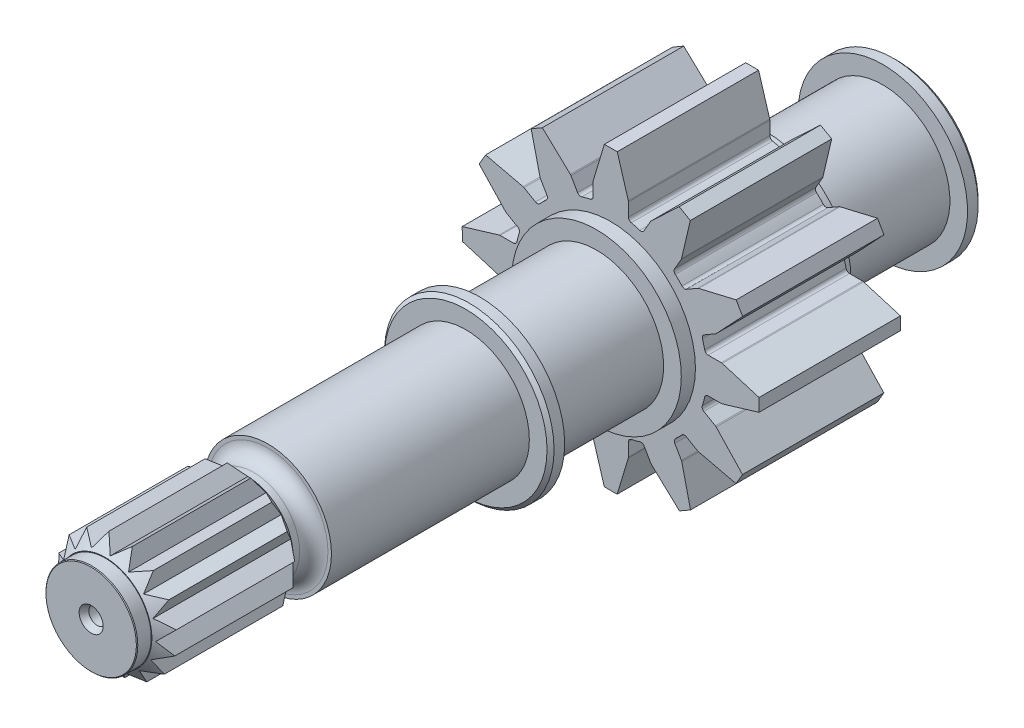
SolidWorks part; units mm, degrees
ref_plane "Спереди" through (0, 0, 0) normal (0, 0, 1) x (1, 0, 0)
ref_plane "Сверху" through (0, 0, 0) normal (0, 1, 0) x (1, 0, 0)
ref_plane "Справа" through (0, 0, 0) normal (1, 0, 0) x (0, 0, -1)
sketch "Эскиз2" plane through (0, 0, 0) normal (0, 0, 1) x (1, 0, 0)
  line L20 (53.7645, -2.946) -> (53.7645, -1.0771)
  line L21 (53.7433, -0.9329) -> (52.1747, 4.2742)
  line L22 (52.1747, 4.2742) -> (50.3546, 4.2742)
  line L23 (50.3546, 4.2742) -> (48.7858, -0.9329)
  line L24 (48.7645, -1.0772) -> (48.7645, -2.9531)
  line L27 (48.7555, -30.4797) -> (48.7555, -32.3473)
  line L28 (48.7768, -32.4916) -> (50.3453, -37.6987)
  line L29 (50.3453, -37.6987) -> (52.1655, -37.6987)
  line L30 (52.1655, -37.6987) -> (53.7343, -32.4916)
  line L31 (53.7555, -32.3473) -> (53.7555, -30.4775)
  line L34 (37.4896, -14.2638) -> (35.6099, -14.2638)
  line L36 (30.2415, -15.8598) -> (30.2586, -17.6738)
  line L37 (30.2586, -17.6738) -> (35.4657, -19.2426)
  line L38 (35.6099, -19.2638) -> (37.5151, -19.2638)
  line L39 (30.2415, -15.8598) -> (35.4656, -14.2851)
  line L41 (65.0289, -19.2139) -> (66.8888, -19.2139)
  line L42 (67.033, -19.1927) -> (72.2401, -17.6241)
  line L43 (72.2401, -17.6241) -> (72.2401, -15.8039)
  line L44 (72.2401, -15.8039) -> (67.033, -14.2352)
  line L45 (66.8887, -14.2139) -> (65.0384, -14.2141)
  line L48 (46.564, -3.5408) -> (45.6287, -1.9209)
  line L49 (45.5382, -1.8066) -> (41.5762, 1.9187)
  line L50 (41.5762, 1.9187) -> (39.9999, 1.0086)
  line L51 (39.9999, 1.0086) -> (41.2449, -4.2853)
  line L52 (41.2986, -4.4209) -> (42.233, -6.0394)
  line L55 (40.6086, -7.6603) -> (38.9805, -6.7203)
  line L56 (38.845, -6.6666) -> (33.5512, -5.4215)
  line L57 (33.5512, -5.4215) -> (32.6411, -6.9978)
  line L58 (32.6411, -6.9978) -> (36.3662, -10.9599)
  line L59 (36.4805, -11.0505) -> (38.0992, -11.985)
  line L62 (38.0961, -21.4251) -> (36.4775, -22.3596)
  line L63 (36.3633, -22.4501) -> (32.638, -26.4121)
  line L64 (32.638, -26.4121) -> (33.5481, -27.9884)
  line L65 (33.5481, -27.9884) -> (38.8378, -26.7444)
  line L66 (38.9806, -26.6864) -> (40.5573, -25.7405)
  line L67 (32.638, -26.4121) -> (36.4137, -22.3964)
  line L69 (42.2473, -27.4181) -> (41.3131, -29.0361)
  line L70 (41.2594, -29.1716) -> (40.0143, -34.4654)
  line L71 (40.0143, -34.4654) -> (41.5906, -35.3755)
  line L72 (41.5906, -35.3755) -> (45.553, -31.6502)
  line L73 (45.6432, -31.5364) -> (46.5897, -29.9013)
  line L76 (55.9807, -29.8805) -> (56.9183, -31.5045)
  line L77 (57.0088, -31.6188) -> (60.9708, -35.344)
  line L78 (60.9708, -35.344) -> (62.5471, -34.434)
  line L79 (62.5471, -34.434) -> (61.3021, -29.1401)
  line L80 (61.2484, -29.0045) -> (60.3134, -27.3849)
  line L83 (61.9386, -25.7577) -> (63.5568, -26.6919)
  line L84 (63.6923, -26.7456) -> (68.9861, -27.9908)
  line L85 (68.9861, -27.9908) -> (69.8962, -26.4145)
  line L86 (69.8962, -26.4145) -> (66.171, -22.4523)
  line L87 (66.0568, -22.3618) -> (64.4371, -21.4267)
  line L90 (64.4528, -12.024) -> (66.0728, -11.0887)
  line L91 (66.1871, -10.9982) -> (69.9123, -7.0362)
  line L92 (69.9123, -7.0362) -> (69.0022, -5.4599)
  line L93 (69.0022, -5.4599) -> (63.7083, -6.7049)
  line L94 (63.5728, -6.7586) -> (61.9545, -7.6929)
  line L97 (60.2872, -6.0251) -> (61.2186, -4.412)
  line L98 (61.2723, -4.2764) -> (62.5174, 1.0174)
  line L99 (62.5174, 1.0174) -> (60.9411, 1.9274)
  line L100 (60.9411, 1.9274) -> (56.979, -1.7977)
  line L101 (56.8884, -1.912) -> (55.9532, -3.5318)
  arc A0 (48.3706, -3.4418) -> (48.7645, -2.9531) centre (48.2645, -2.9531) ccw
  arc A1 (47.1481, -3.7675) -> (46.564, -3.5408) centre (46.997, -3.2908) cw
  arc A2 (48.3706, -3.4418) -> (47.1481, -3.7675) centre (51.2539, -16.7205) ccw
  arc A3 (54.1578, -3.4345) -> (55.3689, -3.7584) centre (51.2539, -16.7205) cw
  arc A4 (60.3845, -6.6456) -> (61.3338, -7.5955) centre (51.2539, -16.7205) cw
  arc A5 (64.2262, -12.6081) -> (64.5499, -13.8206) centre (51.2539, -16.7205) cw
  arc A6 (64.5403, -19.6077) -> (64.2107, -20.8421) centre (51.2539, -16.7205) cw
  arc A7 (61.3184, -25.8547) -> (60.4095, -26.7654) centre (51.2539, -16.7205) cw
  arc A8 (55.3952, -29.6543) -> (54.1489, -29.989) centre (51.2539, -16.7205) cw
  arc A9 (48.362, -29.9912) -> (47.1727, -29.6749) centre (51.2539, -16.7205) cw
  arc A10 (42.1495, -26.7971) -> (41.1853, -25.8337) centre (51.2539, -16.7205) cw
  arc A11 (38.3225, -20.8403) -> (38.0033, -19.6557) centre (51.2539, -16.7205) cw
  arc A12 (37.9785, -13.8689) -> (38.3253, -12.5708) centre (51.2539, -16.7205) cw
  arc A13 (41.2278, -7.5645) -> (42.1358, -6.6599) centre (51.2539, -16.7205) cw
  arc A14 (54.1578, -3.4345) -> (53.7645, -2.946) centre (54.2645, -2.946) cw
  arc A15 (55.3689, -3.7584) -> (55.9532, -3.5318) centre (55.5202, -3.2818) ccw
  arc A16 (60.3845, -6.6456) -> (60.2872, -6.0251) centre (60.7202, -6.2751) cw
  arc A17 (61.9545, -7.6929) -> (61.3338, -7.5955) centre (61.7045, -7.2599) cw
  arc A18 (56.979, -1.7977) -> (56.8884, -1.912) centre (57.3215, -2.162) ccw
  arc A19 (53.7433, -0.9329) -> (53.7645, -1.0771) centre (53.2645, -1.0771) cw
  arc A20 (48.7858, -0.9329) -> (48.7645, -1.0772) centre (49.2645, -1.0772) ccw
  arc A21 (45.5382, -1.8066) -> (45.6287, -1.9209) centre (45.1957, -2.1709) cw
  arc A22 (63.5728, -6.7586) -> (63.7083, -6.7049) centre (63.8228, -7.1916) cw
  arc A23 (61.2723, -4.2764) -> (61.2186, -4.412) centre (60.7856, -4.162) cw
  arc A24 (64.5499, -13.8206) -> (65.0384, -14.2141) centre (65.0384, -13.7141) ccw
  arc A25 (64.2262, -12.6081) -> (64.4528, -12.024) centre (64.7028, -12.457) cw
  arc A26 (66.8887, -14.2139) -> (67.033, -14.2352) centre (66.8888, -14.7139) cw
  arc A27 (66.1871, -10.9982) -> (66.0728, -11.0887) centre (65.8228, -10.6557) cw
  arc A28 (64.5403, -19.6077) -> (65.0289, -19.2139) centre (65.0289, -19.7139) cw
  arc A29 (67.033, -19.1927) -> (66.8888, -19.2139) centre (66.8888, -18.7139) cw
  arc A30 (64.4371, -21.4267) -> (64.2107, -20.8421) centre (64.6871, -20.9937) cw
  arc A31 (66.171, -22.4523) -> (66.0568, -22.3618) centre (65.8068, -22.7948) ccw
  arc A32 (61.3184, -25.8547) -> (61.9386, -25.7577) centre (61.6886, -26.1907) cw
  arc A33 (63.6923, -26.7456) -> (63.5568, -26.6919) centre (63.8068, -26.2589) cw
  arc A34 (60.3134, -27.3849) -> (60.4095, -26.7654) centre (60.7464, -27.1349) cw
  arc A35 (61.3021, -29.1401) -> (61.2484, -29.0045) centre (60.8154, -29.2545) ccw
  arc A36 (56.9183, -31.5045) -> (57.0088, -31.6188) centre (57.3513, -31.2545) ccw
  arc A37 (55.9807, -29.8805) -> (55.3952, -29.6543) centre (55.5477, -30.1305) ccw
  arc A38 (53.7555, -30.4775) -> (54.1489, -29.989) centre (54.2555, -30.4775) cw
  arc A39 (53.7343, -32.4916) -> (53.7555, -32.3473) centre (53.2555, -32.3473) ccw
  arc A40 (48.7555, -32.3473) -> (48.7768, -32.4916) centre (49.2555, -32.3473) ccw
  arc A41 (48.362, -29.9912) -> (48.7555, -30.4797) centre (48.2555, -30.4797) cw
  arc A42 (46.5897, -29.9013) -> (47.1727, -29.6749) centre (47.0224, -30.1518) cw
  arc A43 (45.553, -31.6502) -> (45.6432, -31.5364) centre (45.2105, -31.2859) ccw
  arc A44 (41.3131, -29.0361) -> (41.2594, -29.1716) centre (41.7462, -29.2861) ccw
  arc A45 (42.1495, -26.7971) -> (42.2473, -27.4181) centre (41.8143, -27.1681) cw
  arc A46 (41.1853, -25.8337) -> (40.5573, -25.7405) centre (40.8145, -26.1692) ccw
  arc A47 (38.8378, -26.7444) -> (38.9806, -26.6864) centre (38.7234, -26.2577) ccw
  arc A48 (36.4775, -22.3596) -> (36.3633, -22.4501) centre (36.7275, -22.7926) ccw
  arc A49 (38.0961, -21.4251) -> (38.3225, -20.8403) centre (37.8461, -20.9921) ccw
  arc A50 (37.5151, -19.2638) -> (38.0033, -19.6557) centre (37.5151, -19.7638) cw
  arc A51 (35.4657, -19.2426) -> (35.6099, -19.2638) centre (35.6099, -18.7638) ccw
  arc A52 (35.4656, -14.2851) -> (35.6099, -14.2638) centre (35.6099, -14.7638) cw
  arc A53 (37.9785, -13.8689) -> (37.4896, -14.2638) centre (37.4896, -13.7638) cw
  arc A54 (38.0992, -11.985) -> (38.3253, -12.5708) centre (37.8492, -12.418) cw
  arc A55 (36.3662, -10.9599) -> (36.4805, -11.0505) centre (36.7305, -10.6175) ccw
  arc A56 (38.9805, -6.7203) -> (38.845, -6.6666) centre (38.7305, -7.1534) ccw
  arc A57 (41.2278, -7.5645) -> (40.6086, -7.6603) centre (40.8586, -7.2273) cw
  arc A58 (42.233, -6.0394) -> (42.1358, -6.6599) centre (41.8, -6.2894) cw
  arc A59 (41.2449, -4.2853) -> (41.2986, -4.4209) centre (41.7316, -4.1709) ccw
extrude "Вытянуть1" add sketch "Эскиз2" along normal blind 20 contours L63 A48 L62 A49 A11 A50 L38 A51 L37 L36 L39 A52 L34 A53 A12 A54 L59 A55 L58 L57 L56 A56 L55 A57 A13 A58 L52 A59 L51 L50 L49 A21 L48 A1 A2 A0 L24 A20 L23 L22 L21 A19 L20 A14 A3 A15 L101 A18 L100 L99 L98 A23 L97 A16 A4 A17 L94 A22 L93 L92 L91 A27 L90 A25 A5 A24 L45 A26 L44 L43 L42 A29 L41 A28 A6 A30 L87 A31 L86 L85 L84 A33 L83 A32 A7 A34 L80 A35 L79 L78 L77 A36 L76 A37 A8 A38 L31 A39 L30 L29 L28 A40 L27 A41 A9 A42 L73 A43 L72 L71 L70 A44 L69 A45 A10 A46 L66 A47 L65 L64
sketch "Эскиз3" plane through (0, 0, 0) normal (0, 0, -1) x (-1, 0, 0)
  line L0 (-72.2401, -17.6241) -> (-72.2401, -15.8039) construction
  line L1 (-30.2415, -15.8598) -> (-30.2586, -17.6738) construction
  circle A0 centre (-51.2401, -16.7331) radius 12
  point P2 (-72.2401, -16.714)
  point P7 (-72.2401, -16.714)
  dimension "D1" = 41.9887
  dimension "D2" = 21
extrude "Вытянуть2" add sketch "Эскиз3" along normal blind 2
sketch "Эскиз4" plane through (0, 0, 20) normal (0, 0, 1) x (1, 0, 0)
  circle A0 centre (51.2401, -16.7331) radius 12
extrude "Вытянуть3" add sketch "Эскиз4" along normal blind 2
sketch "Эскиз5" plane through (0, 0, -2) normal (0, 0, -1) x (-1, 0, 0)
  circle A0 centre (-51.2401, -16.7331) radius 9.5
extrude "Вытянуть4" add sketch "Эскиз5" along normal blind 16.5
sketch "Эскиз6" plane through (0, 0, -18.5) normal (0, 0, -1) x (-1, 0, 0)
  circle A0 centre (-51.2401, -16.7331) radius 12
extrude "Вытянуть5" add sketch "Эскиз6" along normal blind 2
chamfer "Фаска2" distance 0.5 angle 45 1 edges at (39.2401, -16.7331, -20.5)
sketch "Эскиз7" plane through (0, 0, 22) normal (0, 0, 1) x (1, 0, 0)
  circle A0 centre (51.2401, -16.7331) radius 9.5
extrude "Вытянуть6" add sketch "Эскиз7" along normal blind 16.5
sketch "Эскиз8" plane through (0, 0, 38.5) normal (0, 0, 1) x (1, 0, 0)
  circle A0 centre (51.2401, -16.7331) radius 12
extrude "Вытянуть7" add sketch "Эскиз8" along normal blind 2
chamfer "Фаска3" distance 0.5 angle 45 1 edges at (63.2401, -16.7331, 40.5)
sketch "Эскиз10" plane through (0, 0, 40.5) normal (0, 0, 1) x (1, 0, 0)
  circle A0 centre (51.2401, -16.7331) radius 9
extrude "Вытянуть9" add sketch "Эскиз10" along normal blind 28
sketch "Эскиз11" plane through (0, 0, 68.5) normal (0, 0, 1) x (1, 0, 0)
  circle A0 centre (51.2401, -16.7331) radius 6.5
extrude "Вытянуть10" add sketch "Эскиз11" along normal blind 3
fillet "Скругление1" radius 2 1 edges at (57.7401, -16.7331, 68.5)
sketch "Эскиз12" plane through (0, 0, 71.5) normal (0, 0, 1) x (1, 0, 0)
  line L1 (52.35, -25.1603) -> (53.458, -23.2305)
  line L2 (53.458, -23.2305) -> (55.4905, -24.0941)
  line L3 (55.4905, -24.0941) -> (55.7757, -21.8871)
  line L4 (55.7757, -21.8871) -> (57.9839, -21.9072)
  line L5 (57.9839, -21.9072) -> (57.4028, -19.7591)
  line L6 (57.4028, -19.7591) -> (59.4506, -18.9326)
  line L7 (59.4506, -18.9326) -> (58.0917, -17.1705)
  line L8 (58.0917, -17.1705) -> (59.6673, -15.6232)
  line L9 (59.6673, -15.6232) -> (57.7375, -14.5152)
  line L10 (57.7375, -14.5152) -> (58.6011, -12.4827)
  line L11 (58.6011, -12.4827) -> (56.3942, -12.1976)
  line L12 (56.3942, -12.1976) -> (56.4142, -9.9893)
  line L13 (56.4142, -9.9893) -> (54.2662, -10.5705)
  line L14 (54.2662, -10.5705) -> (53.4396, -8.5226)
  line L15 (53.4396, -8.5226) -> (51.6775, -9.8816)
  line L16 (51.6775, -9.8816) -> (50.1302, -8.3059)
  line L33 (50.1302, -8.3059) -> (49.0222, -10.2357)
  line L34 (49.0222, -10.2357) -> (46.9897, -9.3721)
  line L35 (46.9897, -9.3721) -> (46.7046, -11.5791)
  line L36 (46.7046, -11.5791) -> (44.4963, -11.559)
  line L37 (44.4963, -11.559) -> (45.0775, -13.7071)
  line L38 (45.0775, -13.7071) -> (43.0296, -14.5336)
  line L39 (43.0296, -14.5336) -> (44.3886, -16.2958)
  line L40 (44.3886, -16.2958) -> (42.8129, -17.843)
  line L41 (42.8129, -17.843) -> (44.7427, -18.951)
  line L42 (44.7427, -18.951) -> (43.8791, -20.9835)
  line L43 (43.8791, -20.9835) -> (46.0861, -21.2686)
  line L44 (46.0861, -21.2686) -> (46.066, -23.4769)
  line L45 (46.066, -23.4769) -> (48.2141, -22.8957)
  line L46 (48.2141, -22.8957) -> (49.0406, -24.9436)
  line L47 (49.0406, -24.9436) -> (50.8028, -23.5847)
  line L48 (50.8028, -23.5847) -> (52.35, -25.1603)
extrude "Вытянуть11" add sketch "Эскиз12" along normal blind 20
sketch "Эскиз13" plane through (0, 0, 91.5) normal (0, 0, 1) x (1, 0, 0)
  circle A0 centre (51.2401, -16.7331) radius 6.5
extrude "Вытянуть12" add sketch "Эскиз13" along normal blind 2
ref_plane "Плоскость1" through (19.9547, 15.3884, 0) normal (-0.7919, -0.6107, 0) x (0, 0, 1)
sketch "Эскиз14" plane through (19.9547, 15.3884, 0) normal (-0.7919, -0.6107, 0) x (0, 0, 1)
  line L0 (71.4516, -40.5204) -> (73.2109, -37.6511)
  line L1 (73.2109, -37.6511) -> (70.7989, -37.6511)
  line L2 (70.7989, -37.6511) -> (71.4516, -40.5204)
sweep "Вырез-По траектории1" cut profiles "Эскиз14" path edge at (57.7401, -16.7331, 71.5)
ref_plane "Плоскость2" through (0, 0, 81.5) normal (0, 0, 1) x (1, 0, 0)
mirror "Зеркальное отражение1" about plane through (0, 0, 81.5) normal (0, 0, 1) of "Вырез-По траектории1"
mirror "Зеркальное отражение2" about plane through (0, 0, 81.5) normal (0, 0, 1) of "Зеркальное отражение1"
chamfer "Фаска5" distance 0.1 angle 45 1 edges at (57.7401, -16.7331, 93.5)
sketch "Эскиз15" plane through (0, 0, -20.5) normal (0, 0, -1) x (-1, 0, 0)
  circle A0 centre (-51.2401, -16.7331) radius 2.5
extrude "Вытянуть13" cut sketch "Эскиз15" against normal blind 74
chamfer "Фаска6" distance 0.5 angle 60 1 edges at (48.7401, -16.7331, -20.5)
ref_plane "Плоскость3" through (40, 0, 0) normal (1, 0, 0) x (0, 0, -1)
sketch "Эскиз16" plane through (40, 0, 0) normal (1, 0, 0) x (0, 0, -1)
  circle A0 centre (-44.6583, -16.3021) radius 1
extrude "Вытянуть14" cut sketch "Эскиз16" along normal blind 9
sketch "Эскиз17" plane through (0, 0, 93.5) normal (0, 0, 1) x (1, 0, 0)
  circle A0 centre (51.2401, -16.7331) radius 1.2
extrude "Вытянуть15" cut sketch "Эскиз17" against normal blind 7
chamfer "Фаска7" distance 0.5 angle 60 1 edges at (52.4401, -16.7331, 93.5)
